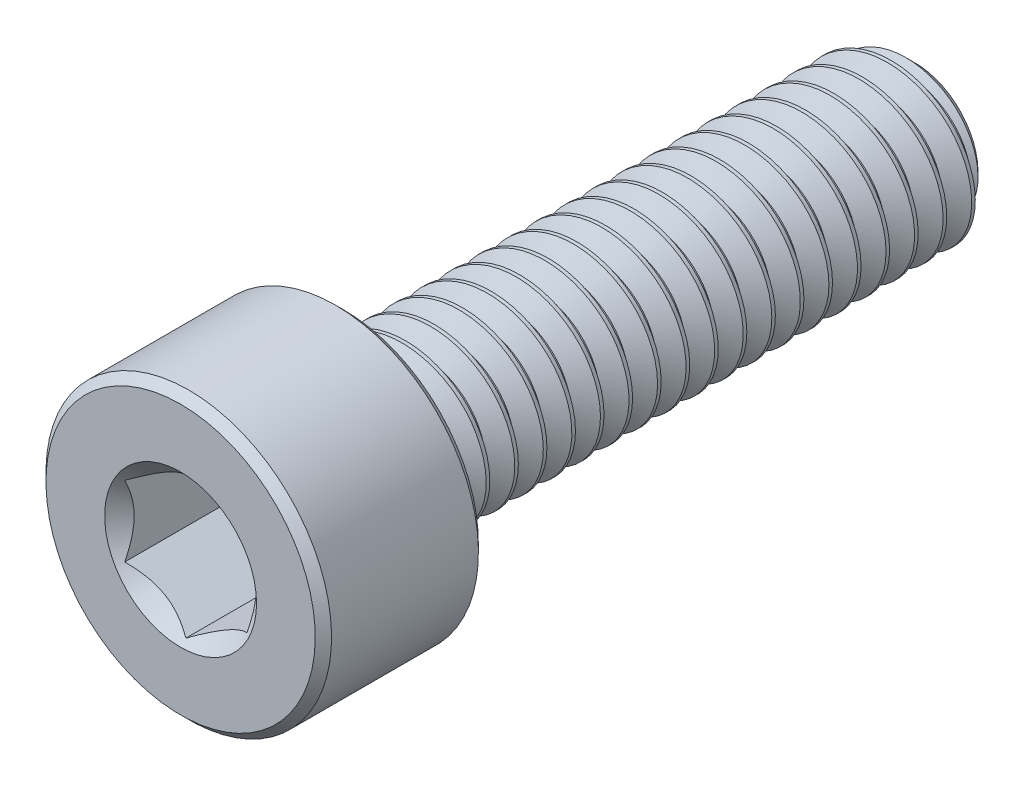
SolidWorks part; units mm, degrees
ref_plane "Front Plane" through (0, 0, 0) normal (0, 0, 1) x (1, 0, 0)
ref_plane "Top Plane" through (0, 0, 0) normal (0, 1, 0) x (1, 0, 0)
ref_plane "Right Plane" through (0, 0, 0) normal (1, 0, 0) x (0, 0, -1)
sketch "Sketch1" plane through (0, 0, 0) normal (1, 0, 0) x (0, 0, -1)
  line L0 (-9, 0) -> (9, 0) construction
  line L1 (9, 0) -> (9, 1.5453) construction
  line L2 (9, 1.5453) -> (8.5453, 2) construction
  line L3 (8.5453, 2) -> (8.475, 2) construction
  line L4 (8.475, 2) -> (-5, 2) construction
  line L5 (-5, 2) -> (-5, 3.5) construction
  line L6 (-5, 3.5) -> (-9, 3.5) construction
  line L7 (-9, 3.5) -> (-9, 0) construction
  line L8 (9, 1.5453) -> (9, 2) construction
  line L9 (8.9562, 2.0758) -> (9.3063, 1.4696) construction
  line L10 (9.3063, 1.4696) -> (9.6562, 2.0758) construction
  line L11 (9.6562, 2.0758) -> (8.9562, 2.0758) construction
  line L12 (9.3063, 2.0758) -> (9.3063, 2) construction
  line L13 (9.3063, 1.4696) -> (9.3063, 1.5453) construction
  line L14 (9.2625, 1.5453) -> (9.35, 1.5453) construction
  line L15 (9, 2) -> (9.6125, 2) construction
  line L16 (8.9781, 2.0379) -> (9.6344, 2.0379) construction
  line L17 (9, 0) -> (9, -2) construction
  line L18 (-5.2, 3.5) -> (-5, 3.3) construction
  line L19 (-8.8, 3.5) -> (-9, 3.3) construction
  line L20 (-5, 2) -> (-5, 0) construction
  line L21 (-5, 1) -> (-0.3333, 1) construction
  line L22 (-0.3333, 1) -> (4.3333, 1) construction
  line L23 (4.3333, 1) -> (9, 1) construction
  line L24 (-0.3333, 1) -> (-0.3333, 2) construction
  line L25 (-0.3333, 2) -> (-0.3333, 3.5) construction
  line L26 (4.3333, 1) -> (4.3333, 3.5) construction
  point P0 (-9, 1.5)
  point P3 (7.25, 2)
  point P4 (0, 0)
  point P18 (4.3333, 2)
  point P22 (9.3063, 1.5453)
  point P24 (8.475, 2)
  point P25 (9.3063, 2)
  point P28 (9.3063, 2.0379)
  point P29 (7.25, -2)
  point P30 (-0.3333, 2)
  point P31 (-7, 3.5)
  point P37 (-5.7, 3.5)
  point P38 (-8.7, 3.5)
  point P45 (-0.3333, 1)
  point P46 (4.3333, 1)
  dimension "D2" = 0.0875
  dimension "D7" = 0.2
  dimension "D8" = 0.2
  dimension "D9" = 0.2
  dimension "D10" = 0.1
  dimension "D11" = 0.5
  dimension "Drive Size" = 3
  dimension "Head Diameter" = 7
  dimension "Head Height" = 4
  dimension "Thread Pitch" = 0.7
  dimension "Thread Dia" = 4
  dimension "Length" = 14
  dimension "D12" = 0.525
  dimension "D4" = 1.75
  dimension "D3" = 45
sketch "Sketch2" plane through (0, 0, 0) normal (1, 0, 0) x (0, 0, -1)
  line L0 (-9, 0) -> (-9, 3.3)
  line L1 (-8.8, 3.5) -> (-5.2, 3.5)
  line L2 (-5, 3.3) -> (-5, 2.2)
  line L4 (8.5453, 2) -> (9, 1.5453)
  line L5 (9, 1.5453) -> (9, 0)
  line L6 (-5, 3.5) -> (-9, 3.5) construction
  line L7 (9, 0) -> (-9, 0)
  line L8 (-8.8, 3.5) -> (-9, 3.3) construction
  line L10 (-8.8, 3.5) -> (-9, 3.3)
  line L14 (-5.2, 3.5) -> (-5, 3.3) construction
  line L16 (-5.2, 3.5) -> (-5, 3.3)
  line L17 (-5, 2) -> (-5, 3.5) construction
  line L19 (-4.8, 2) -> (8.5453, 2)
  line L20 (8.475, 2) -> (-5, 2) construction
  arc A1 (-5, 2.2) -> (-4.8, 2) centre (-4.8, 2.2) ccw
  dimension "D3" = 0.2
revolve "Revolve1" add sketch "Sketch2" angle 360 about L7
sketch "Sketch3" plane through (0, 0, 9) normal (0, 0, 1) x (1, 0, 0)
  line L1 (1.5, -0.866) -> (1.5, 0.866)
  line L2 (1.5, 0.866) -> (0, 1.7321)
  line L3 (0, 1.7321) -> (-1.5, 0.866)
  line L4 (-1.5, 0.866) -> (-1.5, -0.866)
  line L5 (-1.5, -0.866) -> (0, -1.7321)
  line L6 (0, -1.7321) -> (1.5, -0.866)
  circle A0 centre (0, 0) radius 1.5 construction
  circle A1 centre (0, 0) radius 3.5 construction
  circle A2 centre (0, 0) radius 3.5 construction
  circle A3 centre (0, 0) radius 1.7321 construction
  point P13 (0, 0)
  dimension "D1" = 3.4641
extrude "Cut-Extrude1" cut sketch "Sketch3" against normal offset from surface (3 mm away) 1 up to face at (0, 3.3, 5)
sketch "Sketch4" plane through (0, 0, 9) normal (0, 0, 1) x (1, 0, 0)
  circle A0 centre (0, 0) radius 1.862
  dimension "D1" = 3.7239
extrude "Cut-Extrude2" cut sketch "Sketch4" against normal up to vertex (2 mm away) draft 45 up to point (0, 3.5, 7)
sketch "Sketch11" plane through (0, 0, 0) normal (1, 0, 0) x (0, 0, -1)
  line L0 (-9, 0) -> (9, 0) construction
  line L1 (-9, 0) -> (9, 0) construction
  line L2 (-2.375, 0) -> (-2.375, 2) construction
  line L3 (8.475, 2) -> (-5, 2) construction
  line L4 (6.375, 0) -> (6.375, 2) construction
  line L6 (9, 1.5453) -> (9, 2) construction
  point P2 (-2.375, 0)
  point P3 (6.375, 0)
  dimension "D1" = 2.625
  dimension "D2" = 2.625
sketch "Sketch6" plane through (0, 0, -9) normal (0, 0, -1) x (-1, 0, 0)
  circle A0 centre (0, 0) radius 2
curve "Helix/Spiral1" pitch 0.7 height 14.7 turns 21
sketch "Sketch10" plane through (0, 0, 0) normal (1, 0, 0) x (0, 0, -1)
  line L0 (-4.8, -3.5) -> (-4.8, 3.5)
  line L5 (-9, 0) -> (9, 0) construction
  line L6 (-4.8, 2) -> (-4.8, -2) construction
  point P3 (-4.8, 0)
split "Split1" trim tools "Sketch10" bodies to split 106 resulting bodies 114 115
sketch "Sketch7" plane through (0, 0, 0) normal (1, 0, 0) x (0, 0, -1)
  line L0 (8.9781, 2.0379) -> (9.6344, 2.0379)
  line L1 (9.6344, 2.0379) -> (9.35, 1.5453)
  line L2 (9.35, 1.5453) -> (9.2625, 1.5453)
  line L3 (9.2625, 1.5453) -> (8.9781, 2.0379)
sweep "Cut-Sweep1" cut profiles "Sketch7" path "Helix/Spiral1"
sketch "Sketch8" plane through (0, 0, 0) normal (1, 0, 0) x (0, 0, -1)
  line L0 (-5, 0) -> (-5, 2)
  line L1 (-4.8, -2) -> (-4.8, 2) construction
  line L2 (-5, 2) -> (-4.8, 2)
  line L4 (-4.8, 2) -> (-3.6453, 0)
  line L5 (-3.6453, 0) -> (-5, 0)
  line L6 (8.475, 2) -> (-5, 2) construction
  line L7 (-9, 0) -> (9, 0) construction
  dimension "D1" = 60
revolve "Revolve2" add sketch "Sketch8" angle 360 about L5
equation "\"D2@Sketch1\" = \"Thread Pitch@Sketch1\" / 8"
equation "\"D4@Helix/Spiral1\" = \"Thread Pitch@Sketch1\""
equation "\"D7@Sketch1\" = \"Head Height@Sketch1\" * .05"
equation "\"D8@Sketch1\"=\"D7@Sketch1\""
equation "\"D9@Sketch1\"=\"D7@Sketch1\""
equation "\"D10@Sketch1\"=\"D7@Sketch1\"/2"
equation "\"D11@Sketch1\"=\"D10@Sketch1\"*5"
equation "\"D4@Sketch1\"=\"Thread Pitch@Sketch1\"*2.5"
equation "\"D12@Sketch1\"=\"Thread Pitch@Sketch1\"*.75"
equation "\"D3@Helix/Spiral1\"=\"Length@Sketch1\"+\"Thread Pitch@Sketch1\""
equation "\"D3@Sketch2\"=\"Thread Dia@Sketch1\"*0.05"
equation "\"D1@Sketch11\"=\"Length@Sketch1\"*0.1875"
equation "\"D2@Sketch11\"=\"D1@Sketch11\""
equation "\"D1@Sketch4\"=\"D1@Sketch3\"*1.075"
